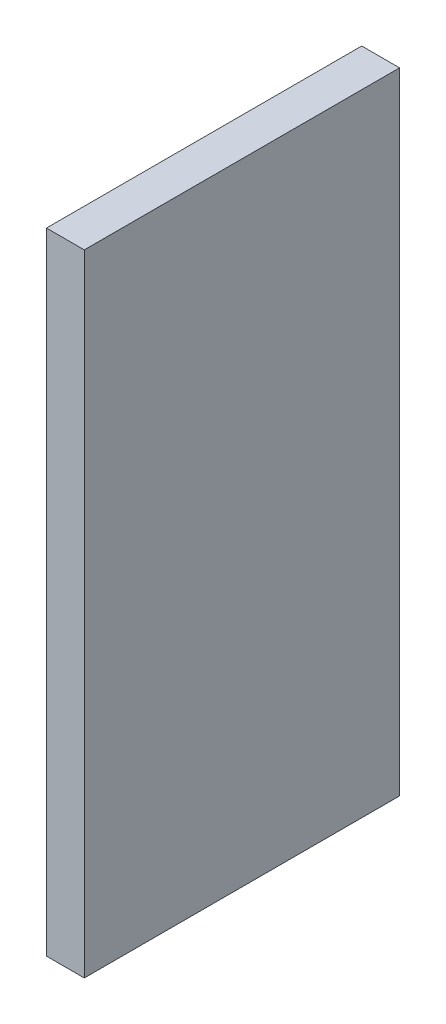
SolidWorks part; units mm, degrees
ref_plane "Front Plane" through (0, 0, 0) normal (0, 0, 1) x (1, 0, 0)
ref_plane "Top Plane" through (0, 0, 0) normal (0, 1, 0) x (1, 0, 0)
ref_plane "Right Plane" through (0, 0, 0) normal (1, 0, 0) x (0, 0, -1)
sketch "Sketch1" plane through (0, 0, 0) normal (1, 0, 0) x (0, 0, -1)
  line L1 (12.5, -25) -> (-12.5, -25)
  line L2 (12.5, -25) -> (12.5, 25)
  line L3 (12.5, 25) -> (-12.5, 25)
  line L4 (-12.5, -25) -> (-12.5, 25)
  line L5 (12.5, -25) -> (-12.5, 25) construction
  line L6 (12.5, 25) -> (-12.5, -25) construction
  point P0 (0, 0)
extrude "Boss-Extrude1" add sketch "Sketch1" along normal blind 3
